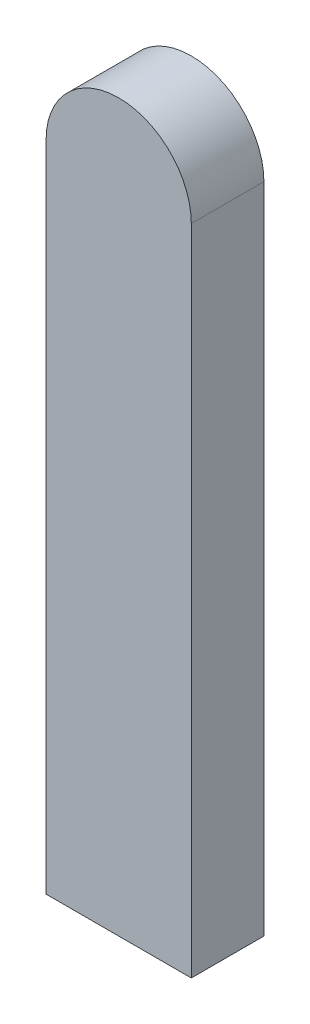
SolidWorks part; units mm, degrees
ref_plane "Front Plane" through (0, 0, 0) normal (0, 0, 1) x (1, 0, 0)
ref_plane "Top Plane" through (0, 0, 0) normal (0, 1, 0) x (1, 0, 0)
ref_plane "Right Plane" through (0, 0, 0) normal (1, 0, 0) x (0, 0, -1)
sketch "Sketch1" plane through (0, 0, 0) normal (0, 0, 1) x (1, 0, 0)
  line L2 (-10, 45) -> (-10, -45)
  line L3 (-10, -45) -> (10, -45)
  line L4 (10, 45) -> (10, -45)
  arc A0 (10, 45) -> (-10, 45) centre (0, 45) ccw
  point P0 (0, 0)
  dimension "D1" = 90
  dimension "D2" = 20
extrude "Boss-Extrude1" add sketch "Sketch1" along normal blind 10
